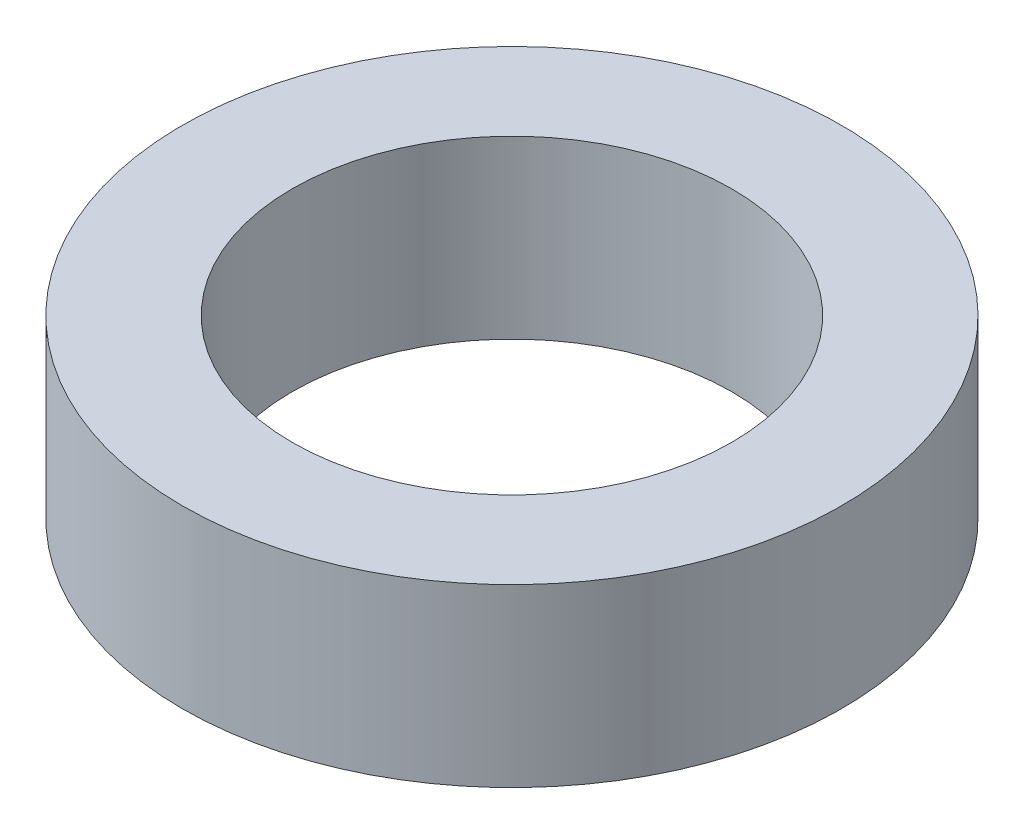
SolidWorks part; units mm, degrees
material "ABS"
ref_plane "Front Plane" through (0, 0, 0) normal (0, 0, 1) x (1, 0, 0)
ref_plane "Top Plane" through (0, 0, 0) normal (0, 1, 0) x (1, 0, 0)
ref_plane "Right Plane" through (0, 0, 0) normal (1, 0, 0) x (0, 0, -1)
sketch "Sketch1" plane through (0, 0, 0) normal (0, 1, 0) x (1, 0, 0)
  circle A0 centre (0, 0) radius 3.175
  circle A1 centre (0, 0) radius 4.7625
  dimension "D1" = 6.35
  dimension "D2" = 9.525
extrude "Boss-Extrude1" add sketch "Sketch1" along normal blind 2.54
